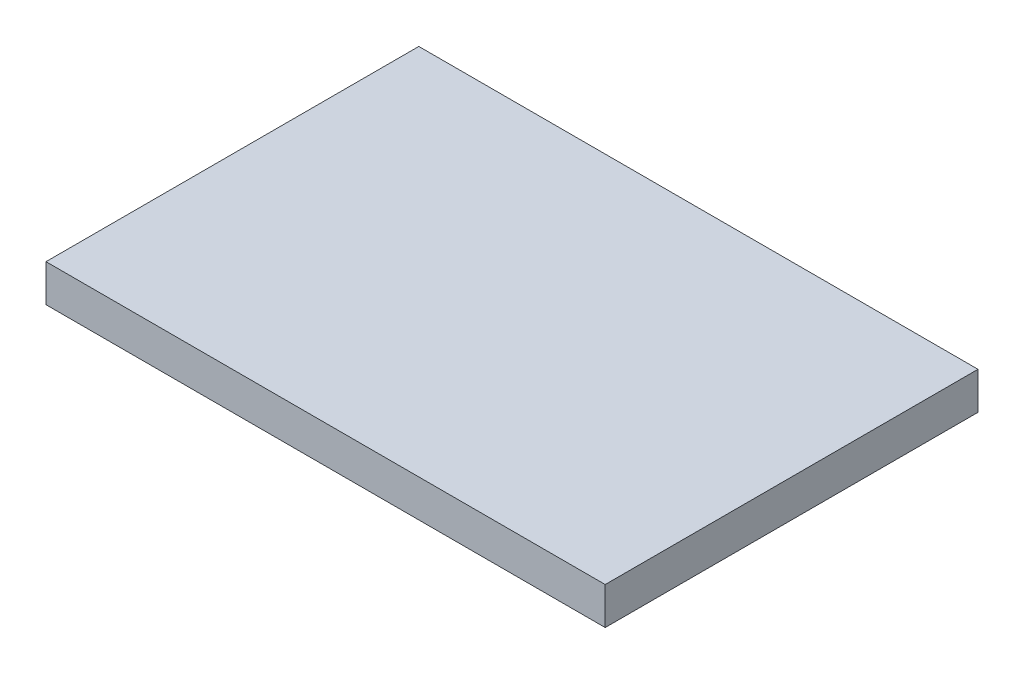
SolidWorks part; units mm, degrees
ref_plane "Front Plane" through (0, 0, 0) normal (0, 0, 1) x (1, 0, 0)
ref_plane "Top Plane" through (0, 0, 0) normal (0, 1, 0) x (1, 0, 0)
ref_plane "Right Plane" through (0, 0, 0) normal (1, 0, 0) x (0, 0, -1)
sketch "Sketch1" plane through (0, 0, 0) normal (0, 1, 0) x (1, 0, 0)
  line L1 (0, 0) -> (75, 0)
  line L2 (0, 0) -> (0, 50)
  line L3 (0, 50) -> (75, 50)
  line L4 (75, 0) -> (75, 50)
  dimension "D1" = 75
  dimension "D2" = 50
extrude "Boss-Extrude1" add sketch "Sketch1" along normal blind 5
